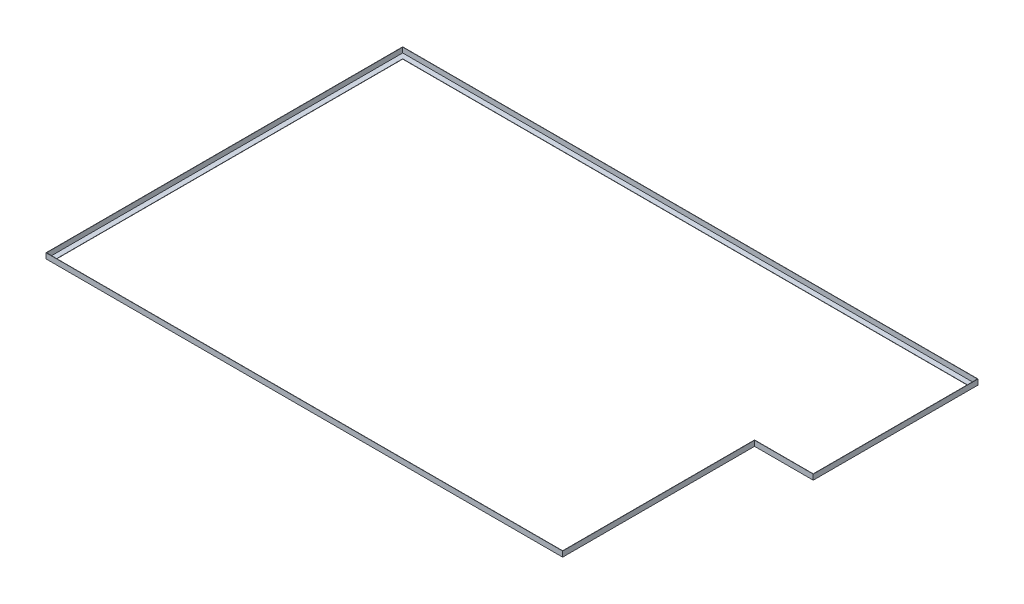
SolidWorks part; units mm, degrees
material "4032-T6"
ref_plane "Front Plane" through (0, 0, 0) normal (0, 0, 1) x (1, 0, 0)
ref_plane "Top Plane" through (0, 0, 0) normal (0, 1, 0) x (1, 0, 0)
ref_plane "Right Plane" through (0, 0, 0) normal (1, 0, 0) x (0, 0, -1)
sketch "Sketch1" plane through (0, 0, 0) normal (0, 1, 0) x (1, 0, 0)
  line L1 (-1459.7204, 836.9572) -> (1334.2796, 836.9572)
  line L2 (-1459.7204, 836.9572) -> (-1459.7204, -915.6428)
  line L3 (-1459.7204, -915.6428) -> (1054.8796, -915.6428)
  line L4 (1334.2796, 836.9572) -> (1334.2796, -1.2428)
  line L5 (-1459.7204, 836.9572) -> (1054.8796, -604.8343) construction
  line L6 (-1459.7204, -915.6428) -> (1334.2796, 836.9572) construction
  line L7 (1054.8796, -1.2428) -> (1334.2796, -1.2428)
  line L8 (1054.8796, -1.2428) -> (1054.8796, -915.6428)
  point P0 (0, 0)
  dimension "D1" = 2794
  dimension "D2" = 1752.6
  dimension "D3" = 279.4
  dimension "D4" = 914.4
  dimension "D5" = 61.928
sketch "Sketch2" plane through (0, 0, 0) normal (1, 0, 0) x (0, 0, -1)
  line L0 (-887.73, 25.4) -> (-887.73, 1.27)
  line L1 (-889, 25.4) -> (-887.73, 25.4)
  line L2 (-889, 25.4) -> (-889, 0)
  line L3 (-889, 0) -> (-863.6, 0)
  line L4 (-863.6, 1.27) -> (-863.6, 0)
  line L7 (-887.73, 1.27) -> (-863.6, 1.27)
  point P5 (-876.3, 0)
  dimension "D1" = 876.3
  dimension "D2" = 25.4
  dimension "D3" = 25.4
  dimension "D4" = 1.27
  dimension "D5" = 1.27
sweep "Sweep1" add profiles "Sketch2" path "Sketch1"
